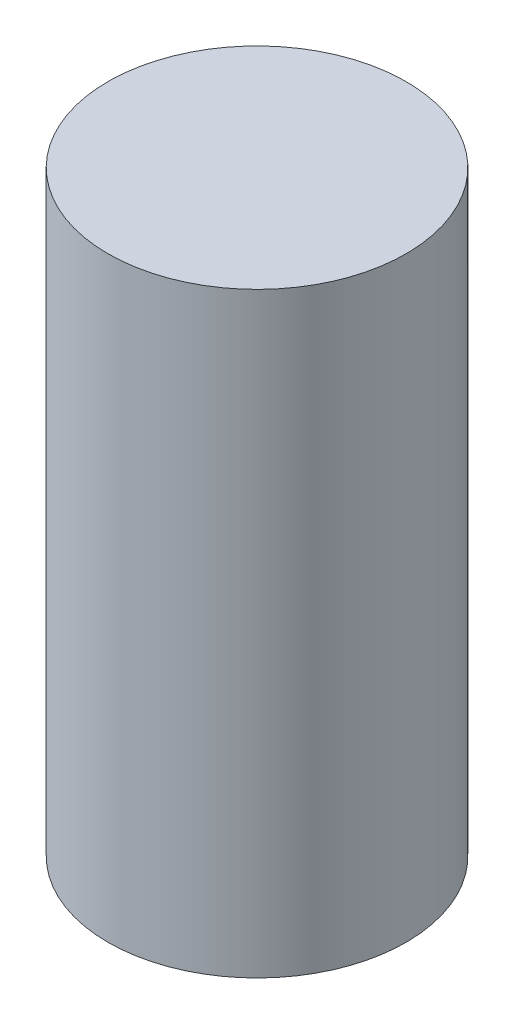
SolidWorks part; units mm, degrees
ref_plane "Front Plane" through (0, 0, 0) normal (0, 0, 1) x (1, 0, 0)
ref_plane "Top Plane" through (0, 0, 0) normal (0, 1, 0) x (1, 0, 0)
ref_plane "Right Plane" through (0, 0, 0) normal (1, 0, 0) x (0, 0, -1)
sketch "Sketch1" plane through (0, 0, 0) normal (0, 1, 0) x (1, 0, 0)
  circle A0 centre (0, 0) radius 5
extrude "Boss-Extrude1" add sketch "Sketch1" along normal blind 20
